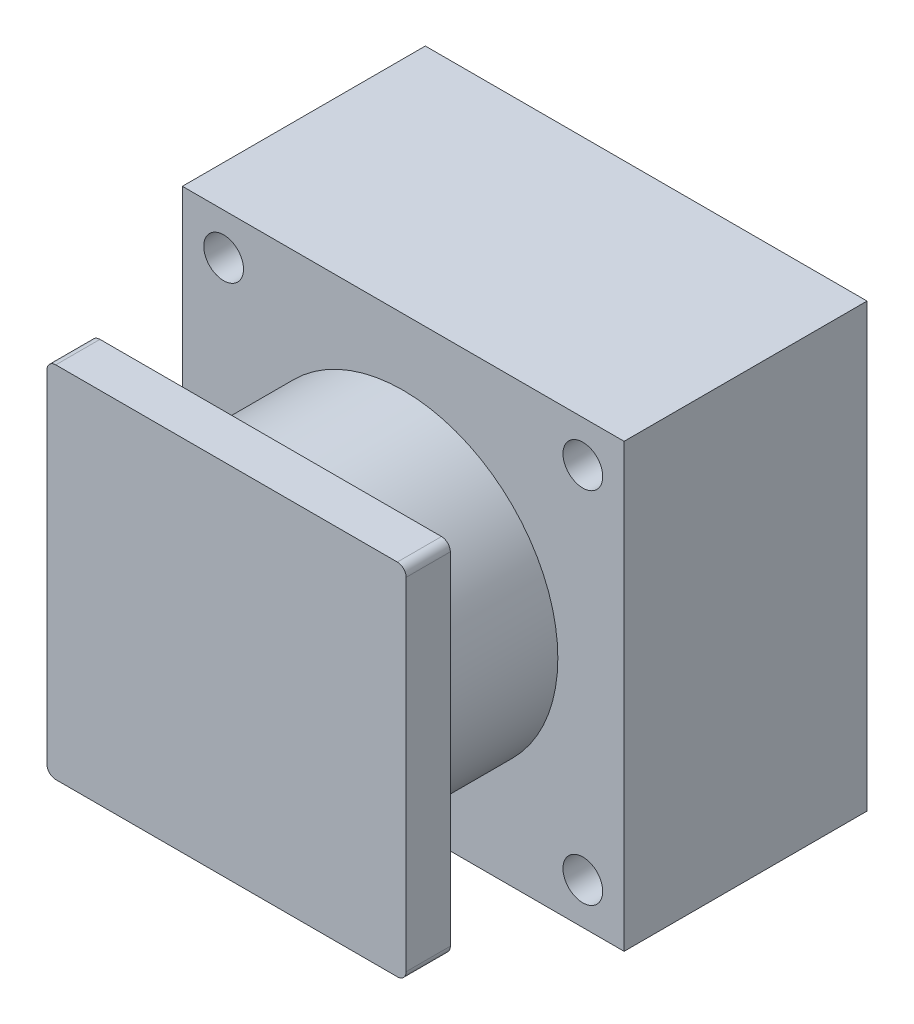
SolidWorks part; units mm, degrees
ref_plane "前视基准面" through (0, 0, 0) normal (0, 0, 1) x (1, 0, 0)
ref_plane "上视基准面" through (0, 0, 0) normal (0, 1, 0) x (1, 0, 0)
ref_plane "右视基准面" through (0, 0, 0) normal (1, 0, 0) x (0, 0, -1)
sketch "草图1" plane through (0, 0, 0) normal (0, 0, 1) x (1, 0, 0)
  line L1 (-50, 50) -> (50, 50)
  line L2 (-50, 50) -> (-50, -50)
  line L3 (-50, -50) -> (50, -50)
  line L4 (50, 50) -> (50, -50)
  line L5 (-50, 50) -> (50, -50) construction
  line L6 (-50, -50) -> (50, 50) construction
  line L7 (-40.6586, 40.6586) -> (40.6586, 40.6586) construction
  line L8 (-40.6586, 40.6586) -> (-40.6586, -40.6586) construction
  line L9 (-40.6586, -40.6586) -> (40.6586, -40.6586) construction
  line L10 (40.6586, 40.6586) -> (40.6586, -40.6586) construction
  line L11 (-40.6586, 40.6586) -> (40.6586, -40.6586) construction
  line L12 (-40.6586, -40.6586) -> (40.6586, 40.6586) construction
  circle A0 centre (-40.6586, 40.6586) radius 4.5
  circle A1 centre (40.6586, 40.6586) radius 4.5
  circle A2 centre (40.6586, -40.6586) radius 4.5
  circle A3 centre (-40.6586, -40.6586) radius 4.5
  circle A4 centre (0, 0) radius 57.5 construction
  point P0 (0, 0)
  point P6 (0, 0)
  dimension "D3" = 9
  dimension "D4" = 115
  dimension "D1" = 100
extrude "凸台-拉伸1" add sketch "草图1" along normal blind 55
sketch "草图2" plane through (0, 0, 55) normal (0, 0, 1) x (1, 0, 0)
  circle A0 centre (0, 0) radius 35
  dimension "D1" = 70
extrude "凸台-拉伸2" add sketch "草图2" along normal blind 30
sketch "草图3" plane through (0, 0, 85) normal (0, 0, 1) x (1, 0, 0)
  line L1 (-40.6586, 40.6586) -> (40.6586, 40.6586)
  line L2 (-40.6586, 40.6586) -> (-40.6586, -40.6586)
  line L3 (-40.6586, -40.6586) -> (40.6586, -40.6586)
  line L4 (40.6586, 40.6586) -> (40.6586, -40.6586)
  line L5 (-40.6586, 40.6586) -> (40.6586, -40.6586) construction
  line L6 (-40.6586, -40.6586) -> (40.6586, 40.6586) construction
  point P0 (0, 0)
extrude "凸台-拉伸3" add sketch "草图3" along normal blind 10
fillet "圆角1" radius 2 4 edges at (40.6586, 40.6586, 90) (40.6586, -40.6586, 90) (-40.6586, 40.6586, 90) (-40.6586, -40.6586, 90)
